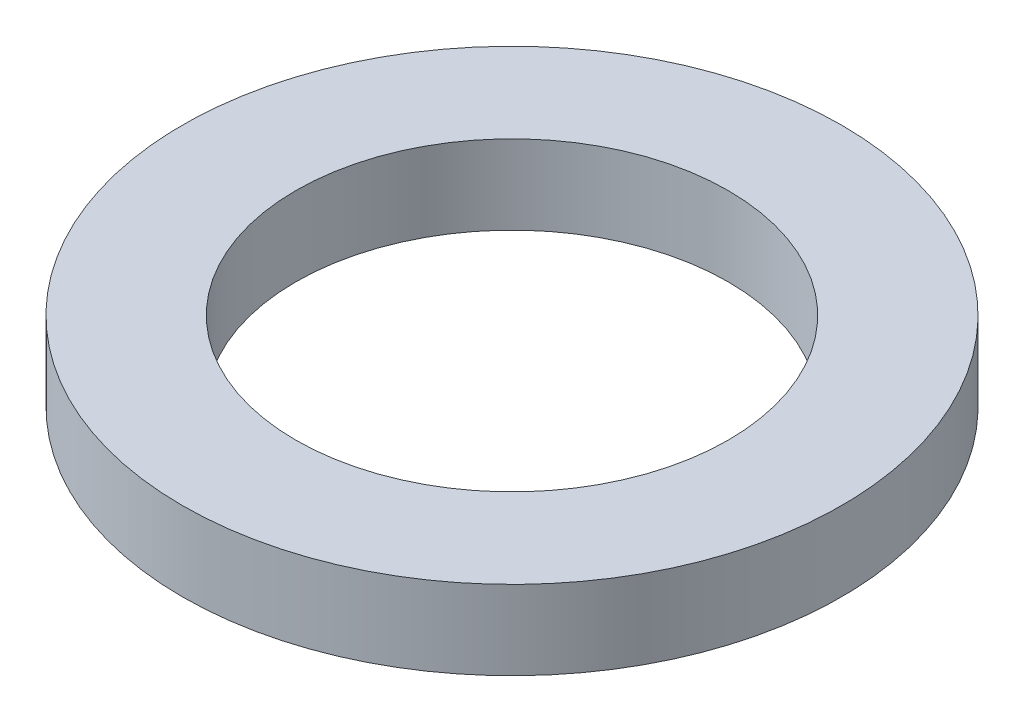
SolidWorks part; units mm, degrees
ref_plane "Front Plane" through (0, 0, 0) normal (0, 0, 1) x (1, 0, 0)
ref_plane "Top Plane" through (0, 0, 0) normal (0, 1, 0) x (1, 0, 0)
ref_plane "Right Plane" through (0, 0, 0) normal (1, 0, 0) x (0, 0, -1)
sketch "Sketch1" plane through (0, 0, 0) normal (0, 1, 0) x (1, 0, 0)
  circle A0 centre (0, 0) radius 25
  dimension "D1" = 50
extrude "Boss-Extrude1" add sketch "Sketch1" along normal blind 6
sketch "Sketch2" plane through (0, 6, 0) normal (0, 1, 0) x (1, 0, 0)
  circle A0 centre (0, 0) radius 16.4
  dimension "D1" = 32.8
extrude "Cut-Extrude1" cut sketch "Sketch2" against normal through all
